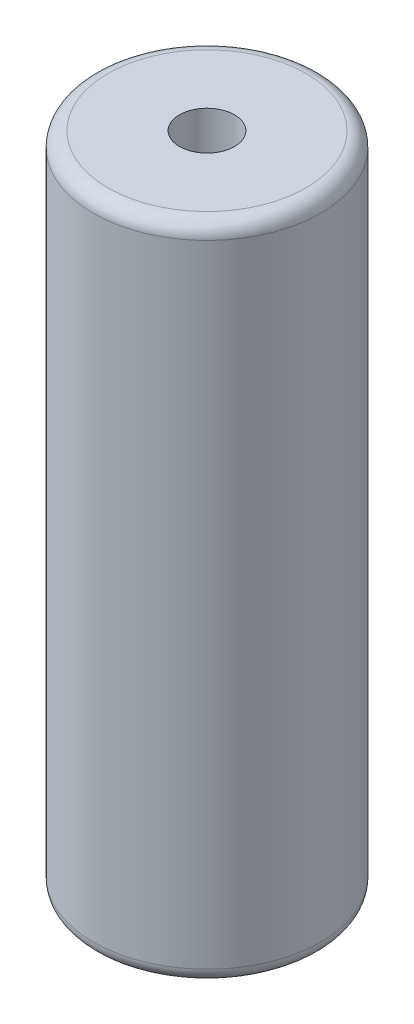
SolidWorks part; units mm, degrees
ref_plane "Plan de face" through (0, 0, 0) normal (0, 0, 1) x (1, 0, 0)
ref_plane "Plan de dessus" through (0, 0, 0) normal (0, 1, 0) x (1, 0, 0)
ref_plane "Plan de droite" through (0, 0, 0) normal (1, 0, 0) x (0, 0, -1)
sketch "Esquisse1" plane through (0, 0, 0) normal (0, 1, 0) x (1, 0, 0)
  circle A0 centre (0, 0) radius 3.1
  circle A1 centre (0, 0) radius 0.75
  dimension "D1" = 6.2
  dimension "D2" = 1.5
extrude "Extrusion1" add sketch "Esquisse1" along normal blind 18
fillet "Congé1" radius 0.4 2 edges at (0, 0, 3.1) (0, 18, 3.1)
